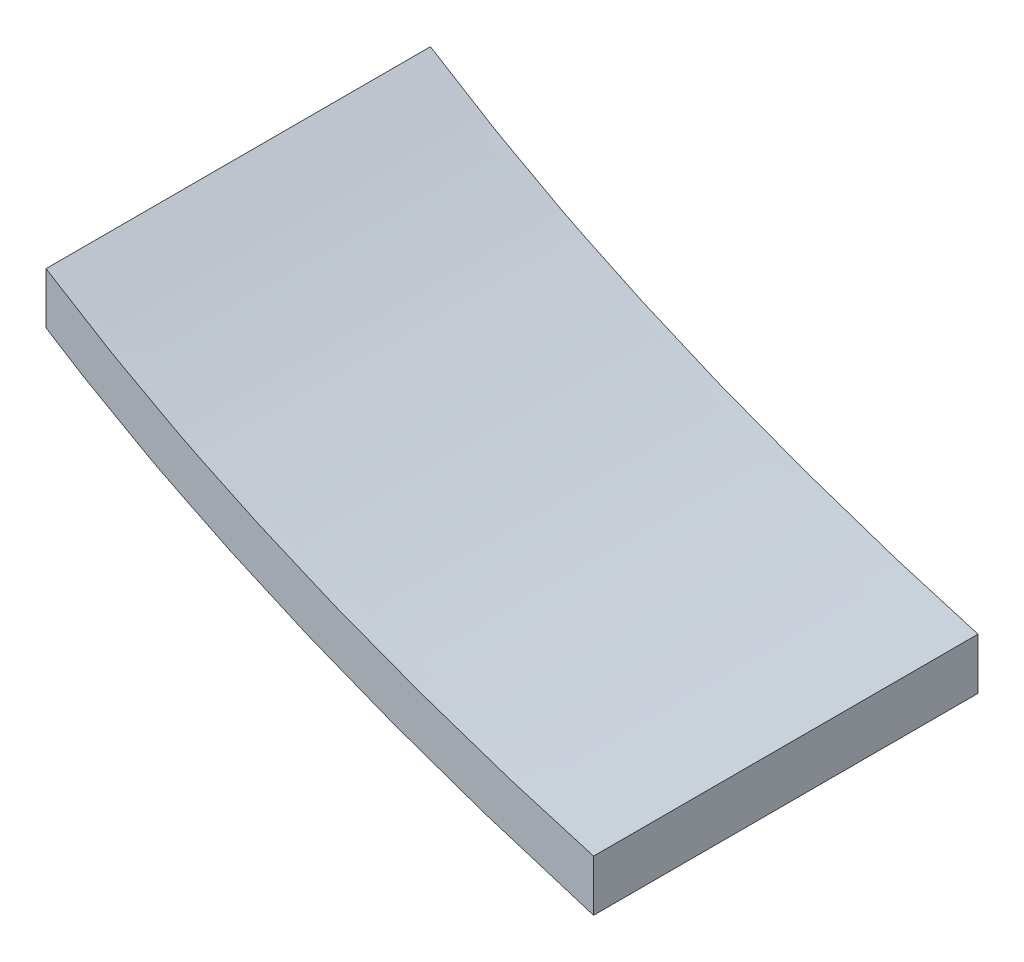
SolidWorks part; units mm, degrees
ref_plane "Front Plane" through (0, 0, 0) normal (0, 0, 1) x (1, 0, 0)
ref_plane "Top Plane" through (0, 0, 0) normal (0, 1, 0) x (1, 0, 0)
ref_plane "Right Plane" through (0, 0, 0) normal (1, 0, 0) x (0, 0, -1)
sketch "Sketch2" plane through (0, 0, 0) normal (0, 0, 1) x (1, 0, 0)
  line L2 (-54.27, 28.3695) -> (-54.27, 23.2895)
  line L3 (0, 0) -> (0, 5.08)
  spline S0 degree 3 poles (0, 5.08) (-2.663, 5.8689) (-5.3373, 6.6612) (-8.0228, 7.4568) (-8.0565, 7.4671) (-8.1126, 7.4846) (-8.1687, 7.5021) (-8.2247, 7.5197) (-8.2583, 7.5306) (-11.2065, 8.5231) (-14.1561, 9.5162) (-17.1071, 10.5096) (-17.1444, 10.5225) (-17.2064, 10.5445) (-17.2684, 10.5666) (-17.3303, 10.5886) (-17.3674, 10.6022) (-20.072, 11.6288) (-22.7783, 12.656) (-25.486, 13.6839) (-25.5274, 13.7001) (-25.5961, 13.728) (-25.6648, 13.7558) (-25.7335, 13.7837) (-25.7745, 13.8008) (-28.2591, 14.8616) (-30.7453, 15.9231) (-33.2333, 16.9854) (-33.2791, 17.0058) (-33.3547, 17.041) (-33.4304, 17.0763) (-33.5061, 17.1115) (-33.5515, 17.1328) (-35.2975, 17.9611) (-37.1388, 18.8345) (-39.0754, 19.7532) (-39.4046, 19.9144) (-40.0883, 20.2601) (-40.6797, 20.559) (-41.1787, 20.8113) (-41.2285, 20.8373) (-41.311, 20.8816) (-41.3935, 20.926) (-41.476, 20.9703) (-41.5254, 20.997) (-43.1142, 21.8612) (-45.0465, 22.9122) (-47.3222, 24.15) (-48.3863, 24.7673) (-50.697, 26.182) (-52.6582, 27.3827) (-54.27, 28.3695) knots 0.044923 0.044923 0.044923 0.044923 0.179184 0.179752 0.18032 0.180888 0.182592 0.18316 0.183728 0.184296 0.333541 0.334177 0.334813 0.335449 0.337357 0.337993 0.338628 0.339264 0.477839 0.478556 0.479272 0.479989 0.482138 0.482855 0.483571 0.484288 0.613447 0.614254 0.615062 0.615869 0.61829 0.619098 0.619905 0.620712 0.712516 0.718422 0.724328 0.730233 0.755454 0.756359 0.757265 0.75817 0.760886 0.761791 0.762697 0.763602 0.849219 0.869027 0.888835 0.908643 1 1 1 1
  spline S1 degree 3 poles (0, 0) (-0.0218, 0.0064) (-0.0485, 0.0142) (-0.0801, 0.0235) (-0.0946, 0.0279) (-3.6284, 1.126) (-7.1686, 2.2262) (-10.7153, 3.3283) (-10.7491, 3.3391) (-10.8052, 3.3575) (-10.8614, 3.3759) (-10.9175, 3.3943) (-10.9511, 3.4057) (-13.903, 4.4433) (-16.8563, 5.4814) (-19.8109, 6.52) (-19.8482, 6.5335) (-19.9103, 6.5564) (-19.9723, 6.5794) (-20.0343, 6.6024) (-20.0714, 6.6165) (-22.7779, 7.6852) (-25.4859, 8.7544) (-28.1955, 9.8243) (-28.2369, 9.8412) (-28.3056, 9.8701) (-28.3743, 9.8991) (-28.443, 9.928) (-28.484, 9.9457) (-30.9687, 11.0458) (-33.455, 12.1466) (-35.943, 13.2482) (-35.9888, 13.2694) (-36.0644, 13.3058) (-36.1401, 13.3423) (-36.2157, 13.3787) (-36.261, 13.4008) (-38.006, 14.2571) (-39.8462, 15.1601) (-41.7817, 16.1099) (-42.1106, 16.2765) (-42.7936, 16.6332) (-43.3843, 16.9418) (-43.8829, 17.2022) (-43.9326, 17.229) (-44.015, 17.2747) (-44.0974, 17.3203) (-44.1797, 17.366) (-44.2291, 17.3936) (-45.8154, 18.2839) (-47.7447, 19.3667) (-50.017, 20.6421) (-51.0789, 21.2771) (-52.4912, 22.1677) (-53.5549, 22.8385) (-54.27, 23.2895) knots 0 0 0 0 0.001094 0.001337 0.00158 0.001823 0.179184 0.179752 0.18032 0.180888 0.182592 0.18316 0.183728 0.184296 0.333541 0.334177 0.334813 0.335449 0.337357 0.337993 0.338628 0.339264 0.477839 0.478556 0.479272 0.479989 0.482138 0.482855 0.483571 0.484288 0.613447 0.614254 0.615062 0.615869 0.61829 0.619098 0.619905 0.620712 0.712516 0.718422 0.724328 0.730233 0.755454 0.756359 0.757265 0.75817 0.760886 0.761791 0.762697 0.763602 0.849219 0.869027 0.888835 0.908643 0.949274 0.949274 0.949274 0.949274
  dimension "D1" = 5.08
extrude "Boss-Extrude1" add sketch "Sketch2" along normal blind 38.1
